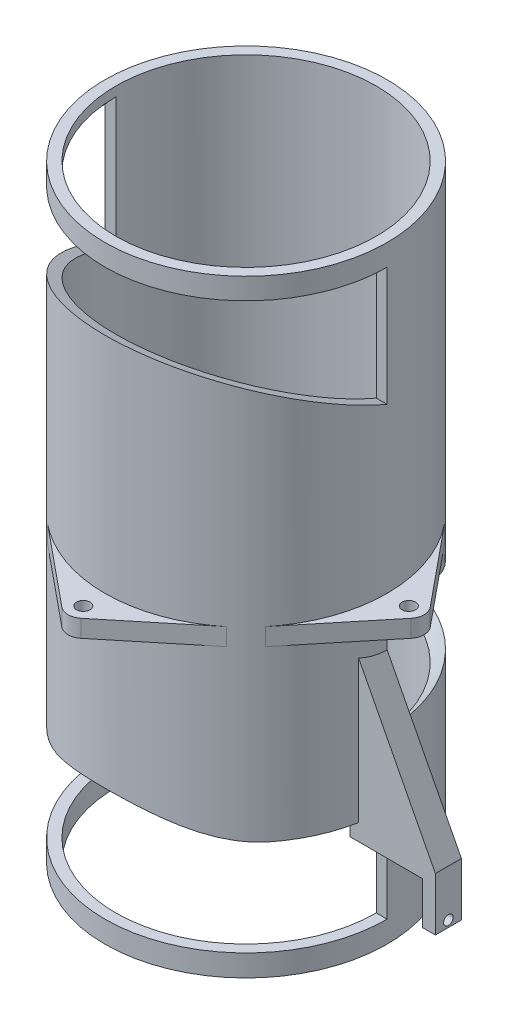
SolidWorks part; units mm, degrees
ref_plane "Front Plane" through (0, 0, 0) normal (0, 0, 1) x (1, 0, 0)
ref_plane "Top Plane" through (0, 0, 0) normal (0, 1, 0) x (1, 0, 0)
ref_plane "Right Plane" through (0, 0, 0) normal (1, 0, 0) x (0, 0, -1)
sketch "Sketch1" plane through (0, 0, 0) normal (0, 1, 0) x (1, 0, 0)
  circle A0 centre (0, 0) radius 30
  circle A1 centre (0, 0) radius 32.5
  dimension "D1" = 60
  dimension "D2" = 65
extrude "Boss-Extrude1" add sketch "Sketch1" along normal blind 140 contours A0
sketch "Sketch2" plane through (0, 0, 0) normal (0, 0, 1) x (1, 0, 0)
  line L0 (-42.5, 107.7161) -> (42.5, 107.7161)
  arc A0 (42.5, 107.7161) -> (-42.5, 107.7161) centre (0, 107.7161) ccw
  dimension "D1" = 85
revolve "Cut-Revolve1" cut sketch "Sketch2" angle 67 about L0
sketch "Sketch3" plane through (0, 0, 0) normal (0, 0, 1) x (1, 0, 0)
  line L0 (-42.5, 70.0763) -> (42.5, 70.0763)
  arc A0 (-42.5, 70.0763) -> (42.5, 70.0763) centre (0, 70.0763) ccw
  dimension "D1" = 85
revolve "Cut-Revolve2" cut sketch "Sketch3" angle 67 about L0
sketch "Sketch4" plane through (0, 140, 0) normal (0, 1, 0) x (1, 0, 0)
  line L0 (-20.605, 25.1333) -> (-2.219, 40.2067)
  line L1 (-40.2067, 2.219) -> (-25.1333, 20.605)
  line L2 (25.1333, 20.605) -> (40.2067, 2.219)
  line L3 (2.219, 40.2067) -> (20.605, 25.1333)
  line L4 (20.605, -25.1333) -> (2.219, -40.2067)
  line L5 (-2.219, -40.2067) -> (-20.605, -25.1333)
  line L6 (-25.1333, -20.605) -> (-40.2067, -2.219)
  line L7 (40.2067, -2.219) -> (25.1333, -20.605)
  circle A0 centre (0, 0) radius 32.5
  circle A1 centre (0, 37.5) radius 3.5
  circle A2 centre (0, 37.5) radius 1.55
  circle A3 centre (0, 0) radius 32.5 construction
  circle A4 centre (37.5, 0) radius 3.5
  circle A5 centre (37.5, 0) radius 1.55
  circle A6 centre (0, -37.5) radius 3.5
  circle A7 centre (0, -37.5) radius 1.55
  circle A8 centre (-37.5, 0) radius 3.5
  circle A9 centre (-37.5, 0) radius 1.55
  point P36 (0, 0)
  dimension "D1" = 3.1
  dimension "D2" = 7
  dimension "D4" = 75
  dimension "D5" = 75
  dimension "D3" = 4
sketch "Sketch5" plane through (0, 0, 0) normal (1, 0, 0) x (0, 0, -1)
  line L0 (-38.4886, 38.605) -> (-38.0879, 37.8284)
  line L1 (-19.9902, 27) -> (0, 27)
  line L2 (-38.4886, 38.605) -> (-38.4886, 5)
  line L3 (-38.4886, 5) -> (0, 5)
  line L4 (0, 27) -> (0, 5)
  line L5 (-32.5, 121.5116) -> (-32.5, 0) construction
  line L6 (-20.3148, 27) -> (-19.9902, 27)
  arc A1 (-38.0879, 37.8284) -> (-20.3148, 27) centre (-20.3148, 47) ccw
  point P11 (-32.5, 27)
  dimension "D3" = 20
  dimension "D1" = 5
  dimension "D2" = 22
extrude "Cut-Extrude1" cut sketch "Sketch5" against normal blind 50 and the other way blind 58
extrude "Boss-Extrude3" add sketch "Sketch4" against normal blind 4 from offset 70 offset against normal yes
sketch "Sketch6" plane through (0, 0, 0) normal (0, 0, 1) x (1, 0, 0)
  line L5 (32.5, 25.67) -> (49.62, 25.67) construction
  line L6 (32.5, 5) -> (32.5, 27) construction
  line L7 (25.3684, 27) -> (32.5, 27) construction
  line L8 (30, 5) -> (30, 27) construction
  line L9 (49.62, 25.67) -> (30, 25.67)
  line L10 (49.62, 25.67) -> (49.62, 23.17)
  line L11 (49.62, 23.17) -> (30, 23.17)
  line L12 (30, 25.67) -> (30, 23.17)
  dimension "D1" = 2.5
  dimension "D2" = 1.33
  dimension "D3" = 17.12
extrude "Boss-Extrude4" add sketch "Sketch6" along normal blind 6
sketch "Sketch7" plane through (49.62, 0, 0) normal (1, 0, 0) x (0, 0, -1)
  line L0 (0, 5) -> (0, 23.17) construction
  line L1 (-6, 23.17) -> (0, 23.17)
  line L2 (-6, 23.17) -> (-6, 13.3968)
  line L3 (-6, 13.3968) -> (0, 13.3968)
  line L4 (0, 23.17) -> (0, 13.3968)
extrude "Boss-Extrude6" add sketch "Sketch7" against normal blind 3
sketch "Sketch8" plane through (0, 0, 0) normal (0, 0, 1) x (1, 0, 0)
  line L0 (32.5, 27) -> (49.62, 25.67)
  line L1 (30, 27) -> (32.5, 27)
  line L2 (30, 27) -> (30, 25.67)
  line L3 (30, 25.67) -> (32.5, 25.67)
  line L4 (32.5, 27) -> (32.5, 25.67)
  line L5 (49.62, 25.67) -> (32.5, 25.67)
  line M5 (30, 27) -> (30, 25.67)
  line M6 (30, 25.67) -> (32.5, 25.67)
  line M7 (32.5, 25.67) -> (32.5, 27)
  line M8 (32.5, 27) -> (30, 27)
extrude "Boss-Extrude7" add sketch "Sketch8" along normal up to surface (6 mm away) contours L5 L0 M7 | M8 M5 M6 M7 up to face at (42.08, 20.7456, 6)
sketch "Sketch9" plane through (49.62, 0, 0) normal (1, 0, 0) x (0, 0, -1)
  line L1 (-6, 25.67) -> (0, 25.67) construction
  circle A0 centre (-3, 14.9138) radius 1.1
  point P2 (-3, 25.67)
  dimension "D1" = 2.2
extrude "Cut-Extrude2" cut sketch "Sketch9" against normal blind 7
sketch "Sketch11" plane through (0, 0, 0) normal (0, 0, 1) x (1, 0, 0)
  line L0 (32.5, 58.7347) -> (49.62, 25.67)
  line L1 (32.5, 42.6902) -> (32.5, 66) construction
rib "Rib3" sketch "Sketch11" sketch "Sketch11" thickness 6 parameters "D1"=6
